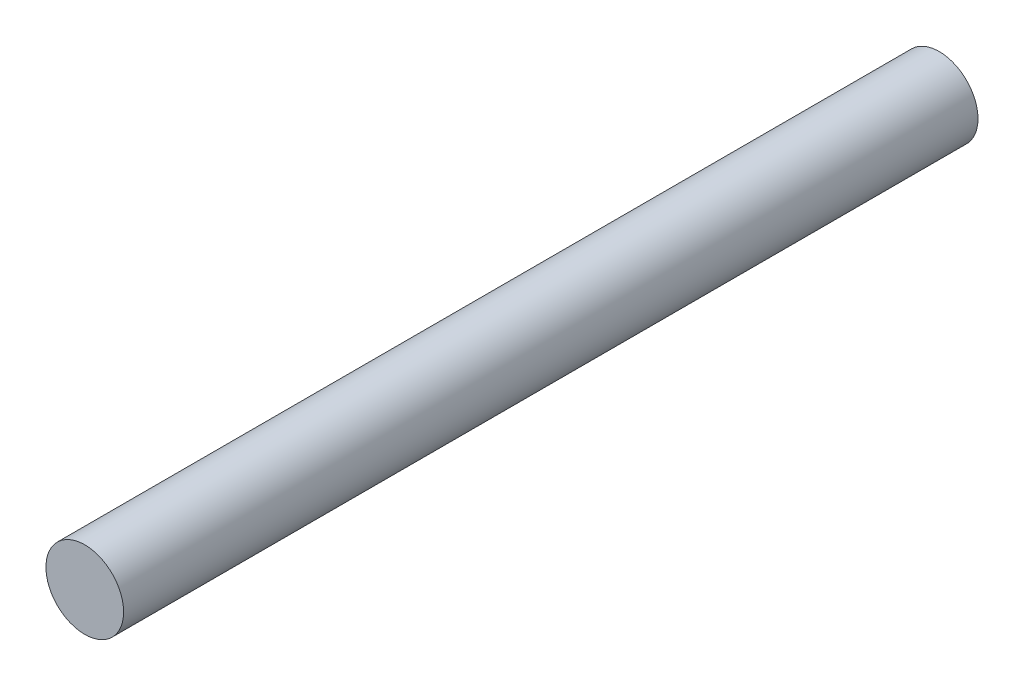
SolidWorks part; units mm, degrees
ref_plane "Front Plane" through (0, 0, 0) normal (0, 0, 1) x (1, 0, 0)
ref_plane "Top Plane" through (0, 0, 0) normal (0, 1, 0) x (1, 0, 0)
ref_plane "Right Plane" through (0, 0, 0) normal (1, 0, 0) x (0, 0, -1)
sketch "Sketch1" plane through (0, 0, 0) normal (0, 0, 1) x (1, 0, 0)
  circle A0 centre (0, 0) radius 2.5
  dimension "D1" = 5
extrude "Boss-Extrude1" add sketch "Sketch1" against normal blind 55
